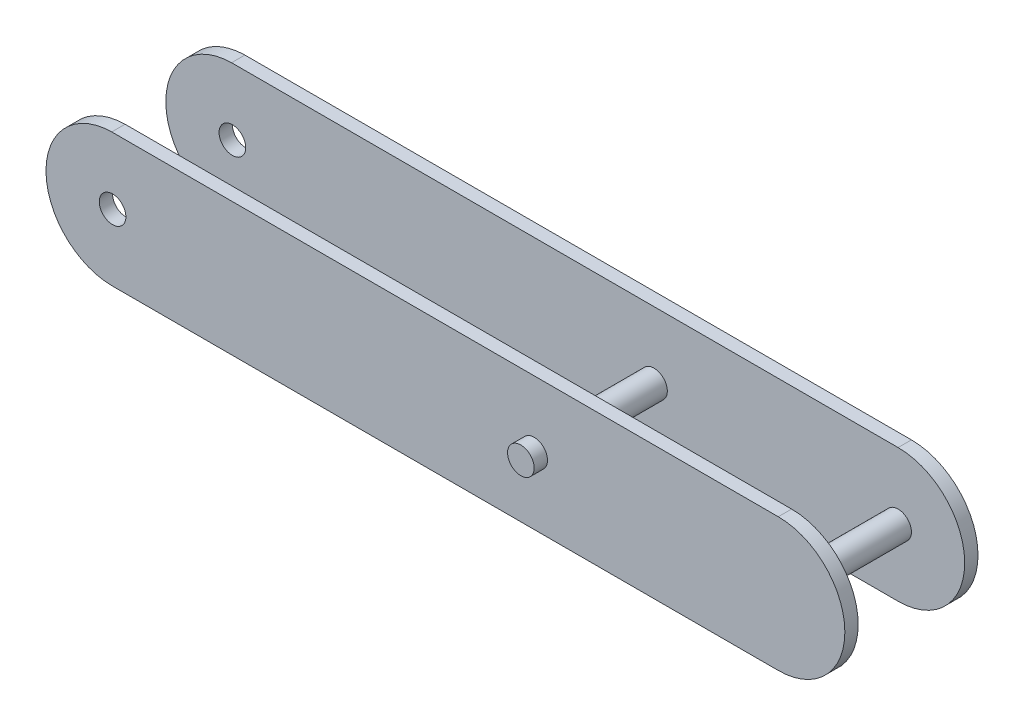
SolidWorks part; units mm, degrees
material "Caucho"
ref_plane "Alzado" through (0, 0, 0) normal (0, 0, 1) x (1, 0, 0)
ref_plane "Planta" through (0, 0, 0) normal (0, 1, 0) x (1, 0, 0)
ref_plane "Vista lateral" through (0, 0, 0) normal (1, 0, 0) x (0, 0, -1)
sketch "Croquis2" plane through (0, 0, 0) normal (0, 0, 1) x (1, 0, 0)
  circle A0 centre (0, 0) radius 3
extrude "Saliente-Extruir1" add sketch "Croquis2" along normal blind 18
sketch "Croquis3" plane through (0, 0, 0) normal (0, 0, 1) x (1, 0, 0)
  circle A0 centre (0, 0) radius 3
extrude "Saliente-Extruir2" add sketch "Croquis3" against normal blind 18
ref_plane "Plano1" through (0, 0, 0) normal (1, 0, 0) x (0, 0, -1)
sketch "Croquis4" plane through (0, 0, 0) normal (1, 0, 0) x (0, 0, -1)
  line L0 (0, 0) -> (0, 15)
  line L2 (12, 15) -> (15, 15)
  line L3 (15, 15) -> (15, -15)
  line L4 (15, -15) -> (12, -15)
  line L5 (12, -15) -> (12, 15)
  line L6 (-12, -15) -> (-12, 15)
  line L8 (-15, -15) -> (-12, -15)
  line L9 (-15, 15) -> (-15, -15)
  line L10 (-12, 15) -> (-15, 15)
extrude "Saliente-Extruir3" add sketch "Croquis4" against normal blind 110 contours L6 L10 L9 L8 | L5 L4 L3 L2
sketch "Croquis5" plane through (0, 0, 0) normal (1, 0, 0) x (0, 0, -1)
  line L0 (-15, 15) -> (-12, 15)
  line L1 (-12, 15) -> (-12, -15)
  line L2 (-12, -15) -> (-15, -15)
  line L3 (-15, -15) -> (-15, 15)
  line L4 (12, 15) -> (15, 15)
  line L5 (15, 15) -> (15, -15)
  line L6 (15, -15) -> (12, -15)
  line L7 (12, -15) -> (12, 15)
extrude "Saliente-Extruir4" add sketch "Croquis5" along normal blind 70
ref_plane "Plano2" through (0, 0, 15) normal (0, 0, 1) x (1, 0, 0)
sketch "Croquis6" plane through (0, 0, 15) normal (0, 0, 1) x (1, 0, 0)
  line L0 (-95.185, -15) -> (-94.815, -15) construction
  line L2 (-110, -15) -> (-94.815, -15)
  line L3 (-110, 15) -> (70, 15) construction
  line L6 (-95, 0) -> (-95.0925, 0) construction
  line L9 (-95.185, 15) -> (-110, 15)
  line L10 (-110, 15) -> (-110, -15)
  arc A0 (-95.185, 15) -> (-94.815, -15) centre (-95, 0) ccw
extrude "Cortar-Extruir1" cut sketch "Croquis6" against normal blind 70 contours A0 L10 L2 | A0 L9 L10
sketch "Croquis7" plane through (0, 0, 15) normal (0, 0, 1) x (1, 0, 0)
  line L0 (70, 15) -> (55, 15) construction
  line L6 (55, -15) -> (70, -15)
  line L7 (70, -15) -> (70, 15)
  line L8 (70, 15) -> (55, 15)
  arc A0 (55, -15) -> (55, 15) centre (55, 0) ccw
extrude "Cortar-Extruir2" cut sketch "Croquis7" against normal blind 70 contours A0 L7 L8 | A0 L6 L7
sketch "Croquis8" plane through (0, 0, 15) normal (0, 0, 1) x (1, 0, 0)
  circle A0 centre (-95, 0) radius 3
extrude "Cortar-Extruir3" cut sketch "Croquis8" against normal blind 70
sketch "Croquis9" plane through (0, 0, 15) normal (0, 0, 1) x (1, 0, 0)
  line L0 (55, 15) -> (55, -15) construction
  circle A0 centre (55, 0) radius 3
extrude "Saliente-Extruir6" add sketch "Croquis9" against normal blind 30
